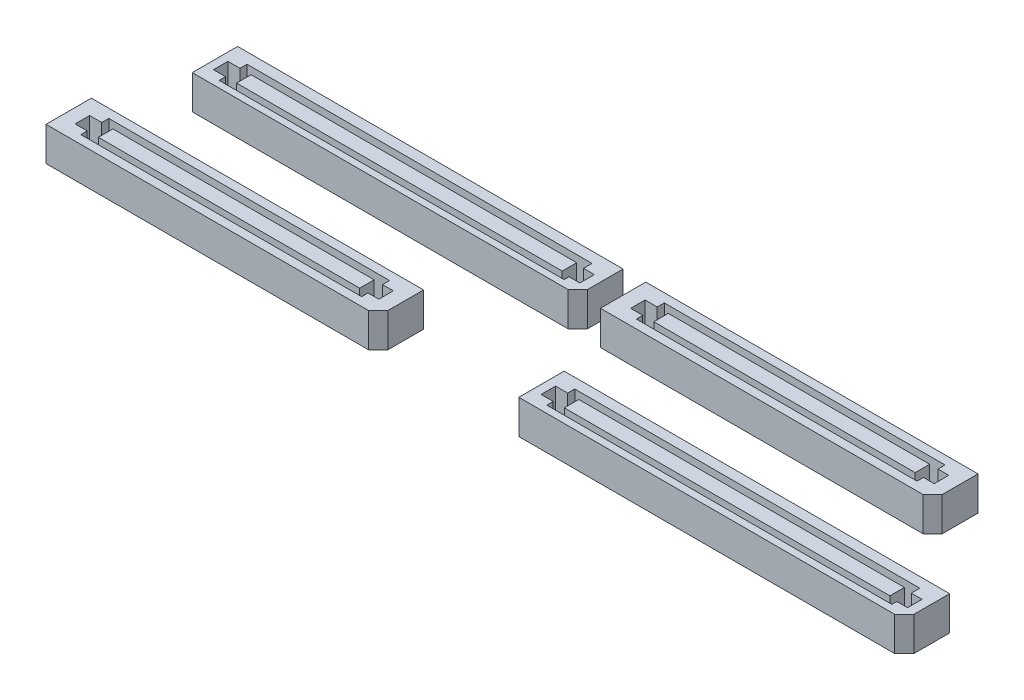
SolidWorks part; units mm, degrees
ref_plane "Front Plane" through (0, 0, 0) normal (0, 0, 1) x (1, 0, 0)
ref_plane "Top Plane" through (0, 0, 0) normal (0, 1, 0) x (1, 0, 0)
ref_plane "Right Plane" through (0, 0, 0) normal (1, 0, 0) x (0, 0, -1)
ref_plane "Plane1" through (0, -1.6866, 0) normal (0, 1, 0) x (1, 0, 0)
ref_plane "center-of-slot" through (0, -0.8433, 0) normal (0, 1, 0) x (1, 0, 0)
sketch "Sketch1" plane through (0, 0, 0) normal (0, 1, 0) x (1, 0, 0)
  line L0 (55.811, 9.5) -> (97.25, 9.5)
  line L1 (3.686, 9.5) -> (39.25, 9.5)
  line L2 (2.625, 8.439) -> (2.625, 4.5)
  line L3 (2.625, 4.5) -> (39.25, 4.5) construction
  line L4 (39.25, 9.5) -> (39.25, 4.5) construction
  line L5 (0, 0) -> (100, 0) construction
  line L6 (0, 0) -> (0, 75) construction
  line L7 (0, 75) -> (100, 75) construction
  line L8 (100, 0) -> (100, 75) construction
  line L9 (54.75, 8.439) -> (54.75, 4.5)
  line L10 (54.75, 4.5) -> (97.25, 4.5) construction
  line L11 (97.25, 9.5) -> (97.25, 4.5) construction
  line L12 (51.811, 22.5) -> (87.375, 22.5)
  line L13 (6.811, 22.5) -> (48.25, 22.5)
  line L14 (5.75, 21.439) -> (5.75, 17.5)
  line L15 (5.75, 17.5) -> (48.25, 17.5) construction
  line L16 (48.25, 22.5) -> (48.25, 17.5) construction
  line L17 (50.75, 21.439) -> (50.75, 17.5)
  line L18 (50.75, 17.5) -> (87.375, 17.5) construction
  line L19 (87.375, 22.5) -> (87.375, 17.5) construction
  line L20 (5.75, 21.439) -> (6.811, 22.5) construction
  line L21 (50.75, 21.439) -> (51.811, 22.5) construction
  line L22 (54.75, 8.439) -> (55.811, 9.5) construction
  line L23 (2.625, 8.439) -> (3.686, 9.5) construction
  line L24 (2.625, 4.5) -> (38.195, 4.5)
  line L25 (38.195, 4.5) -> (39.25, 5.555)
  line L26 (39.25, 5.555) -> (39.25, 9.5)
  line L27 (50.75, 17.5) -> (86.32, 17.5)
  line L28 (86.32, 17.5) -> (87.375, 18.555)
  line L29 (87.375, 18.555) -> (87.375, 22.5)
  line L30 (54.75, 4.5) -> (96.19, 4.5)
  line L31 (96.19, 4.5) -> (97.25, 5.56)
  line L32 (97.25, 5.56) -> (97.25, 9.5)
  line L33 (5.75, 17.5) -> (47.19, 17.5)
  line L34 (47.19, 17.5) -> (48.25, 18.56)
  line L35 (48.25, 18.56) -> (48.25, 22.5)
  line L36 (5.75, 21.439) -> (5.75, 22.5)
  line L37 (5.75, 22.5) -> (6.811, 22.5)
  line L38 (2.625, 8.439) -> (2.625, 9.5)
  line L39 (2.625, 9.5) -> (3.686, 9.5)
  line L40 (54.75, 8.439) -> (54.75, 9.5)
  line L41 (54.75, 9.5) -> (55.811, 9.5)
  line L42 (50.75, 21.439) -> (50.75, 22.5)
  line L43 (50.75, 22.5) -> (51.811, 22.5)
  point P0 (2.625, 9.5)
  point P9 (54.75, 9.5)
  point P13 (5.75, 22.5)
  point P17 (50.75, 22.5)
extrude "SV" add sketch "Sketch1" along normal blind 3.75
sketch "Sketch3" plane through (0, 3.75, 0) normal (0, 1, 0) x (1, 0, 0)
  line L0 (4.1893, 7.7457) -> (5.5243, 7.7457)
  line L1 (4.1893, 8.5242) -> (37.667, 8.5242) construction
  line L2 (4.1893, 8.5242) -> (4.1893, 5.4386) construction
  line L3 (4.1893, 5.4386) -> (37.667, 5.4386) construction
  line L4 (37.667, 8.5242) -> (37.667, 5.4386) construction
  line L5 (5.5243, 7.7457) -> (5.5243, 8.5242)
  line L6 (5.5243, 8.5242) -> (36.4757, 8.5242)
  line L7 (36.4757, 8.5242) -> (36.4757, 7.7457)
  line L8 (36.4757, 7.7457) -> (37.667, 7.7457)
  line L9 (37.667, 7.7457) -> (37.667, 6.1479)
  line L10 (37.667, 6.1479) -> (36.4757, 6.1479)
  line L11 (36.4757, 6.1479) -> (36.4757, 5.4386)
  line L12 (36.4757, 5.4386) -> (5.5243, 5.4386)
  line L13 (5.5243, 5.4386) -> (5.5243, 6.1479)
  line L14 (5.5243, 6.1479) -> (4.1893, 6.1479)
  line L15 (4.1893, 6.1479) -> (4.1893, 7.7457)
  line L16 (52.4211, 20.7536) -> (53.7561, 20.7536)
  line L17 (6.7471, 7.7457) -> (35.5588, 7.7457)
  line L18 (6.7471, 7.7457) -> (6.7471, 6.1479)
  line L19 (6.7471, 6.1479) -> (35.5588, 6.1479)
  line L20 (35.5588, 7.7457) -> (35.5588, 6.1479)
  line L21 (52.4211, 21.532) -> (85.8988, 21.532) construction
  line L22 (52.4211, 21.532) -> (52.4211, 18.4464) construction
  line L23 (52.4211, 18.4464) -> (85.8988, 18.4464) construction
  line L24 (85.8988, 21.532) -> (85.8988, 18.4464) construction
  line L25 (53.7561, 20.7536) -> (53.7561, 21.532)
  line L26 (53.7561, 21.532) -> (84.7075, 21.532)
  line L27 (84.7075, 21.532) -> (84.7075, 20.7536)
  line L28 (84.7075, 20.7536) -> (85.8988, 20.7536)
  line L29 (85.8988, 20.7536) -> (85.8988, 19.1558)
  line L30 (85.8988, 19.1558) -> (84.7075, 19.1558)
  line L31 (84.7075, 19.1558) -> (84.7075, 18.4464)
  line L32 (84.7075, 18.4464) -> (53.7561, 18.4464)
  line L33 (53.7561, 18.4464) -> (53.7561, 19.1558)
  line L34 (53.7561, 19.1558) -> (52.4211, 19.1558)
  line L35 (52.4211, 19.1558) -> (52.4211, 20.7536)
  line L36 (54.9789, 20.7536) -> (83.7906, 20.7536)
  line L37 (54.9789, 20.7536) -> (54.9789, 19.1558)
  line L38 (54.9789, 19.1558) -> (83.7906, 19.1558)
  line L39 (83.7906, 20.7536) -> (83.7906, 19.1558)
  line L40 (55.7059, 7.599) -> (57.0409, 7.599)
  line L41 (55.7059, 8.3775) -> (96.2696, 8.3775) construction
  line L42 (55.7059, 8.3775) -> (55.7059, 5.2919) construction
  line L43 (55.7059, 5.2919) -> (96.2696, 5.2919) construction
  line L44 (96.2696, 8.3775) -> (96.2696, 5.2919) construction
  line L45 (57.0409, 7.599) -> (57.0409, 8.3775)
  line L46 (57.0409, 8.3775) -> (95.0783, 8.3775)
  line L47 (95.0783, 8.3775) -> (95.0783, 7.4377)
  line L48 (95.0783, 7.4377) -> (96.2696, 7.4377)
  line L49 (96.2696, 7.4377) -> (96.2696, 5.8399)
  line L50 (96.2696, 5.8399) -> (95.0783, 5.8399)
  line L51 (95.0783, 5.8399) -> (95.0783, 5.2919)
  line L52 (95.0783, 5.2919) -> (57.0409, 5.2919)
  line L53 (57.0409, 5.2919) -> (57.0409, 6.0012)
  line L54 (57.0409, 6.0012) -> (55.7059, 6.0012)
  line L55 (55.7059, 6.0012) -> (55.7059, 7.599)
  line L56 (58.2637, 7.599) -> (94.1615, 7.599)
  line L57 (58.2637, 7.599) -> (58.2637, 6.0012)
  line L58 (58.2637, 6.0012) -> (94.1615, 6.0012)
  line L59 (94.1615, 7.599) -> (94.1615, 6.0012)
  line L60 (6.6366, 20.5397) -> (7.9716, 20.5397)
  line L61 (6.6366, 21.3182) -> (47.2003, 21.3182) construction
  line L62 (6.6366, 21.3182) -> (6.6366, 18.2325) construction
  line L63 (6.6366, 18.2325) -> (47.2003, 18.2325) construction
  line L64 (47.2003, 21.3182) -> (47.2003, 18.2325) construction
  line L65 (7.9716, 20.5397) -> (7.9716, 21.3182)
  line L66 (7.9716, 21.3182) -> (46.009, 21.3182)
  line L67 (46.009, 21.3182) -> (46.009, 20.3784)
  line L68 (46.009, 20.3784) -> (47.2003, 20.3784)
  line L69 (47.2003, 20.3784) -> (47.2003, 18.7806)
  line L70 (47.2003, 18.7806) -> (46.009, 18.7806)
  line L71 (46.009, 18.7806) -> (46.009, 18.2325)
  line L72 (46.009, 18.2325) -> (7.9716, 18.2325)
  line L73 (7.9716, 18.2325) -> (7.9716, 18.9419)
  line L74 (7.9716, 18.9419) -> (6.6366, 18.9419)
  line L75 (6.6366, 18.9419) -> (6.6366, 20.5397)
  line L76 (9.1944, 20.5397) -> (45.0922, 20.5397)
  line L77 (9.1944, 20.5397) -> (9.1944, 18.9419)
  line L78 (9.1944, 18.9419) -> (45.0922, 18.9419)
  line L79 (45.0922, 20.5397) -> (45.0922, 18.9419)
extrude "Cut-Extrude1" cut sketch "Sketch3" against normal blind 3.5
sketch "Sketch6" [suppressed] plane through (0, -1.6866, 0) normal (0, 1, 0) x (1, 0, 0)
  line L0 (2.625, 4.5) -> (2.625, 9.5) construction
  line L1 (5.75, 22.5) -> (48.25, 22.5) construction
  line L2 (5.75, 22.5) -> (5.75, 17.5) construction
  line L3 (5.75, 17.5) -> (48.25, 17.5) construction
  line L4 (48.25, 22.5) -> (48.25, 17.5) construction
  line L5 (50.75, 22.5) -> (87.375, 22.5) construction
  line L6 (50.75, 22.5) -> (50.75, 17.5) construction
  line L7 (50.75, 17.5) -> (87.375, 17.5) construction
  line L8 (87.375, 22.5) -> (87.375, 17.5) construction
  line L9 (97.25, 9.5) -> (54.75, 9.5) construction
  line L10 (97.25, 9.5) -> (97.25, 4.5) construction
  line L11 (97.25, 4.5) -> (54.75, 4.5) construction
  line L12 (54.75, 9.5) -> (54.75, 4.5) construction
  line L13 (39.25, 9.5) -> (2.625, 9.5) construction
  line L14 (39.25, 9.5) -> (39.25, 4.5) construction
  line L15 (39.25, 4.5) -> (2.625, 4.5) construction
  line L16 (2.625, 9.5) -> (2.625, 4.5) construction
  line L17 (2.625, 4.5) -> (38.195, 4.5)
  line L18 (2.625, 9.5) -> (39.25, 9.5) construction
  line L19 (48.25, 18.5619) -> (47.1881, 17.5) construction
  line L20 (39.25, 5.555) -> (39.25, 9.5)
  line L21 (48.25, 18.5619) -> (48.25, 22.5)
  line L22 (47.1881, 17.5) -> (5.75, 17.5)
  line L23 (39.25, 5.555) -> (38.195, 4.5) construction
  line L24 (54.75, 4.5) -> (96.19, 4.5)
  line L25 (96.19, 4.5) -> (97.25, 5.56) construction
  line L26 (97.25, 5.56) -> (97.25, 9.5)
  line L27 (50.75, 17.5) -> (86.32, 17.5)
  line L28 (86.32, 17.5) -> (87.375, 18.555) construction
  line L29 (87.375, 18.555) -> (87.375, 22.5)
  line L30 (2.625, 4.5) -> (2.625, 8.44)
  line L31 (2.625, 8.44) -> (3.685, 9.5)
  line L32 (3.685, 9.5) -> (39.25, 9.5)
  line L33 (5.75, 17.5) -> (5.75, 21.44)
  line L34 (5.75, 21.44) -> (6.81, 22.5)
  line L35 (6.81, 22.5) -> (48.25, 22.5)
  line L36 (54.75, 4.5) -> (54.75, 8.44)
  line L37 (54.75, 8.44) -> (55.81, 9.5)
  line L38 (55.81, 9.5) -> (97.25, 9.5)
  line L39 (87.375, 22.5) -> (51.805, 22.5)
  line L40 (51.805, 22.5) -> (50.75, 21.445)
  line L41 (50.75, 21.445) -> (50.75, 17.5)
  line L42 (47.1881, 17.5) -> (48.25, 17.5)
  line L43 (48.25, 17.5) -> (48.25, 18.5619)
  line L44 (38.195, 4.5) -> (39.25, 4.5)
  line L45 (39.25, 4.5) -> (39.25, 5.555)
  line L46 (96.19, 4.5) -> (97.25, 4.5)
  line L47 (97.25, 4.5) -> (97.25, 5.56)
  line L48 (86.32, 17.5) -> (87.375, 17.5)
  line L49 (87.375, 17.5) -> (87.375, 18.555)
  point P0 (5.75, 22.5)
  point P6 (50.75, 22.5)
  point P15 (54.75, 9.5)
extrude "SV4(a)" [suppressed] add sketch "Sketch6" against normal blind 5 separate body
sketch "Sketch7" [suppressed] plane through (0, -5.6866, 0) normal (0, -1, 0) x (1, 0, 0)
  line L0 (7.9716, -21.3182) -> (7.9716, -20.5397)
  line L1 (7.9716, -20.5397) -> (6.6366, -20.5397)
  line L2 (6.6366, -20.5397) -> (6.6366, -18.9419)
  line L3 (6.6366, -18.9419) -> (7.9716, -18.9419)
  line L4 (7.9716, -18.9419) -> (7.9716, -18.2325)
  line L6 (7.9716, -18.2325) -> (46.009, -18.2325)
  line L7 (46.009, -18.2325) -> (46.009, -18.7806)
  line L8 (46.009, -18.7806) -> (47.2003, -18.7806)
  line L9 (47.2003, -18.7806) -> (47.2003, -20.3784)
  line L10 (47.2003, -20.3784) -> (46.009, -20.3784)
  line L11 (46.009, -20.3784) -> (46.009, -21.3182)
  line L12 (46.009, -21.3182) -> (7.9716, -21.3182)
  line L13 (53.7561, -21.532) -> (84.7075, -21.532)
  line L14 (9.1944, -20.5397) -> (45.0922, -20.5397)
  line L15 (9.1944, -20.5397) -> (9.1944, -18.9419)
  line L16 (9.1944, -18.9419) -> (45.0922, -18.9419)
  line L17 (45.0922, -20.5397) -> (45.0922, -18.9419)
  line L18 (54.9789, -20.7536) -> (83.7906, -20.7536)
  line L19 (54.9789, -20.7536) -> (54.9789, -19.1558)
  line L20 (54.9789, -19.1558) -> (83.7906, -19.1558)
  line L21 (83.7906, -20.7536) -> (83.7906, -19.1558)
  line L22 (94.1615, -7.599) -> (58.2637, -7.599)
  line L23 (94.1615, -7.599) -> (94.1615, -6.0012)
  line L24 (94.1615, -6.0012) -> (58.2637, -6.0012)
  line L25 (58.2637, -7.599) -> (58.2637, -6.0012)
  line L26 (35.5588, -7.7457) -> (6.7471, -7.7457)
  line L27 (35.5588, -7.7457) -> (35.5588, -6.1479)
  line L28 (35.5588, -6.1479) -> (6.7471, -6.1479)
  line L29 (6.7471, -7.7457) -> (6.7471, -6.1479)
  line L30 (84.7075, -21.532) -> (84.7075, -20.7536)
  line L31 (84.7075, -20.7536) -> (85.8988, -20.7536)
  line L32 (85.8988, -20.7536) -> (85.8988, -19.1558)
  line L33 (85.8988, -19.1558) -> (84.7075, -19.1558)
  line L34 (84.7075, -19.1558) -> (84.7075, -18.4464)
  line L35 (84.7075, -18.4464) -> (53.7561, -18.4464)
  line L36 (53.7561, -18.4464) -> (53.7561, -19.1558)
  line L37 (53.7561, -19.1558) -> (52.4211, -19.1558)
  line L38 (52.4211, -19.1558) -> (52.4211, -20.7536)
  line L39 (52.4211, -20.7536) -> (53.7561, -20.7536)
  line L40 (53.7561, -20.7536) -> (53.7561, -21.532)
  line L41 (57.0409, -8.3775) -> (57.0409, -7.599)
  line L42 (57.0409, -7.599) -> (55.7059, -7.599)
  line L43 (55.7059, -7.599) -> (55.7059, -6.0012)
  line L44 (55.7059, -6.0012) -> (57.0409, -6.0012)
  line L45 (57.0409, -6.0012) -> (57.0409, -5.2919)
  line L46 (57.0409, -5.2919) -> (95.0783, -5.2919)
  line L47 (95.0783, -5.2919) -> (95.0783, -5.8399)
  line L48 (95.0783, -5.8399) -> (96.2696, -5.8399)
  line L49 (96.2696, -5.8399) -> (96.2696, -7.4377)
  line L50 (96.2696, -7.4377) -> (95.0783, -7.4377)
  line L51 (95.0783, -7.4377) -> (95.0783, -8.3775)
  line L52 (95.0783, -8.3775) -> (57.0409, -8.3775)
  line L53 (4.1893, -6.1479) -> (5.5243, -6.1479)
  line L54 (5.5243, -6.1479) -> (5.5243, -5.4386)
  line L55 (5.5243, -5.4386) -> (36.4757, -5.4386)
  line L56 (36.4757, -5.4386) -> (36.4757, -6.1479)
  line L57 (36.4757, -6.1479) -> (37.667, -6.1479)
  line L58 (37.667, -6.1479) -> (37.667, -7.7457)
  line L59 (37.667, -7.7457) -> (36.4757, -7.7457)
  line L60 (36.4757, -7.7457) -> (36.4757, -8.5242)
  line L61 (36.4757, -8.5242) -> (5.5243, -8.5242)
  line L62 (5.5243, -8.5242) -> (5.5243, -7.7457)
  line L63 (5.5243, -7.7457) -> (4.1893, -7.7457)
  line L64 (4.1893, -7.7457) -> (4.1893, -6.1479)
extrude "SV4(b)" [suppressed] add sketch "Sketch7" along normal blind 3.5
